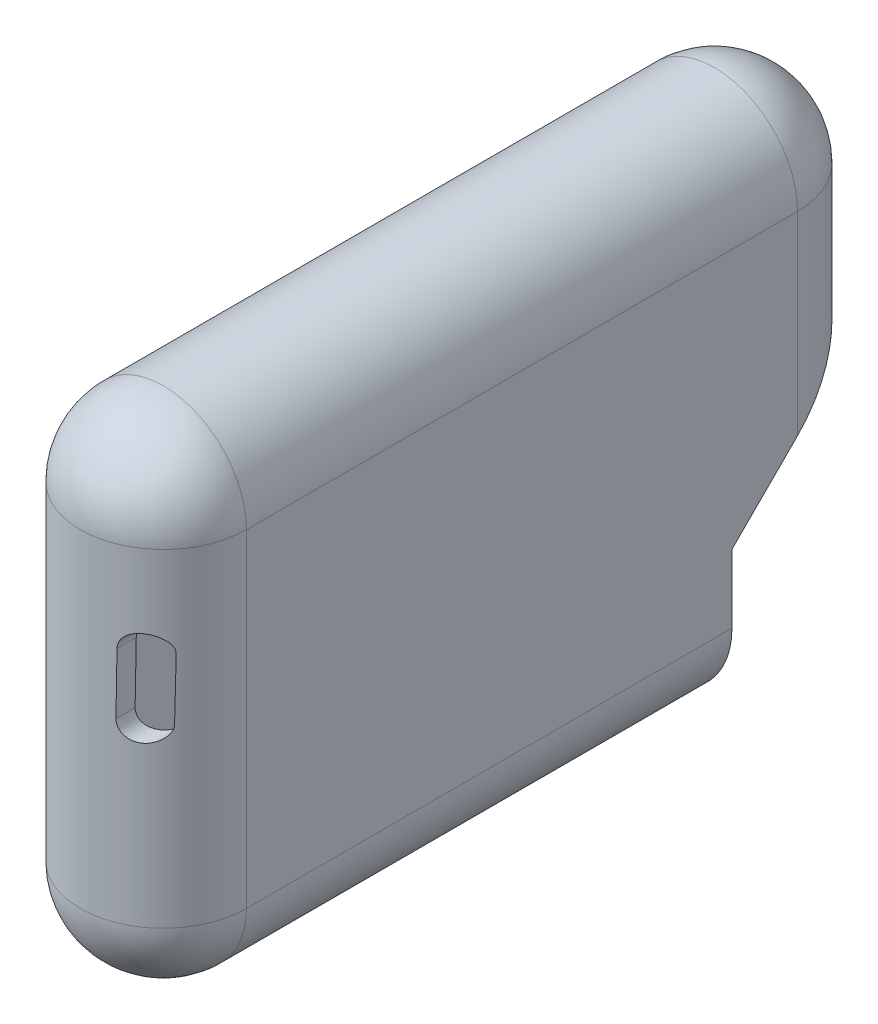
SolidWorks part; units mm, degrees
ref_plane "Front Plane" through (0, 0, 0) normal (0, 0, 1) x (1, 0, 0)
ref_plane "Top Plane" through (0, 0, 0) normal (0, 1, 0) x (1, 0, 0)
ref_plane "Right Plane" through (0, 0, 0) normal (1, 0, 0) x (0, 0, -1)
sketch "Sketch1" plane through (0, 0, 0) normal (0, 0, 1) x (1, 0, 0)
  line L0 (-1.1087, 18.0382) -> (-1.1087, -19.4618) construction
  line L5 (6.3913, 18.0382) -> (6.3913, -19.4618)
  line L6 (-8.6087, 18.0382) -> (-8.6087, -19.4618)
  arc A0 (6.3913, 18.0382) -> (-8.6087, 18.0382) centre (-1.1087, 18.0382) ccw
  arc A1 (-8.6087, -19.4618) -> (6.3913, -19.4618) centre (-1.1087, -19.4618) ccw
  point P1 (-1.1087, -0.7118)
  point P9 (0, 0)
  point P10 (7.6942, -25.282)
  point P11 (-0.4791, -20.1787)
  point P13 (-1.1087, 25.5382)
  dimension "D1" = 15
  dimension "D2" = 45
extrude "Extrude-Thin1" add sketch "Sketch1" along normal blind 8 and the other way blind 55 thin thin type one direction wall 2
sketch "Sketch3" plane through (0, 0, 8) normal (0, 0, 1) x (1, 0, 0)
  line L0 (-1.1087, 27.5382) -> (-1.1087, -28.9618) construction
  line L1 (6.3913, -19.4618) -> (6.3913, 18.0382) construction
  line L2 (8.3913, -19.4618) -> (8.3913, 18.0382) construction
  line L3 (6.3913, -19.4618) -> (6.3913, 18.0382)
  line L4 (8.3913, -19.4618) -> (8.3913, 18.0382)
  line L5 (-1.1087, 27.5382) -> (-1.1087, 25.5382)
  line L6 (-1.1087, -26.9618) -> (-1.1087, -28.9618)
  arc A0 (8.3913, 18.0382) -> (-10.6087, 18.0382) centre (-1.1087, 18.0382) ccw construction
  arc A1 (-10.6087, -19.4618) -> (8.3913, -19.4618) centre (-1.1087, -19.4618) ccw construction
  arc A2 (-8.6087, -19.4618) -> (6.3913, -19.4618) centre (-1.1087, -19.4618) ccw construction
  arc A3 (6.3913, 18.0382) -> (-8.6087, 18.0382) centre (-1.1087, 18.0382) ccw construction
  arc A4 (-1.1087, -26.9618) -> (6.3913, -19.4618) centre (-1.1087, -19.4618) ccw
  arc A5 (-1.1087, -28.9618) -> (8.3913, -19.4618) centre (-1.1087, -19.4618) ccw
  arc A6 (6.3913, 18.0382) -> (-1.1087, 25.5382) centre (-1.1087, 18.0382) ccw
  arc A7 (8.3913, 18.0382) -> (-1.1087, 27.5382) centre (-1.1087, 18.0382) ccw
revolve "Revolve1" add sketch "Sketch3" angle 180 about L0
ref_plane "Plane1" through (-1.1087, -19.4618, 17.5) normal (0, 0, 1) x (1, 0, 0)
sketch "Sketch4" plane through (-1.1087, -19.4618, 17.5) normal (0, 0, 1) x (1, 0, 0)
  line L0 (5.4685, 27.125) -> (5.3835, 20.1693) construction
  line L1 (7.4132, 27.1012) -> (7.3282, 20.1455)
  line L2 (3.5238, 27.1487) -> (3.4388, 20.193)
  arc A0 (7.4132, 27.1012) -> (3.5238, 27.1487) centre (5.4685, 27.125) ccw
  arc A1 (3.4388, 20.193) -> (7.3282, 20.1455) centre (5.3835, 20.1693) ccw
  point P4 (5.426, 23.6471)
extrude "Cut-Extrude1" cut sketch "Sketch4" against normal through all both and the other way through all
sketch "Sketch5" plane through (0, 0, -55) normal (0, 0, -1) x (-1, 0, 0)
  line L0 (1.1087, -28.9618) -> (1.1087, 27.5382) construction
  line L1 (-6.3913, -19.4618) -> (-6.3913, 18.0382) construction
  line L2 (-8.3913, -19.4618) -> (-8.3913, 18.0382) construction
  line L3 (-6.3913, -19.4618) -> (-6.3913, 18.0382)
  line L4 (-8.3913, -19.4618) -> (-8.3913, 18.0382)
  line L5 (1.1087, -28.9618) -> (1.1087, -26.9618)
  line L6 (1.1087, 25.5382) -> (1.1087, 27.5382)
  arc A0 (-8.3913, -19.4618) -> (10.6087, -19.4618) centre (1.1087, -19.4618) ccw construction
  arc A1 (10.6087, 18.0382) -> (-8.3913, 18.0382) centre (1.1087, 18.0382) ccw construction
  arc A2 (-6.3913, -19.4618) -> (8.6087, -19.4618) centre (1.1087, -19.4618) ccw construction
  arc A3 (8.6087, 18.0382) -> (-6.3913, 18.0382) centre (1.1087, 18.0382) ccw construction
  arc A4 (-6.3913, -19.4618) -> (1.1087, -26.9618) centre (1.1087, -19.4618) ccw
  arc A5 (1.1087, 25.5382) -> (-6.3913, 18.0382) centre (1.1087, 18.0382) ccw
  arc A6 (1.1087, 27.5382) -> (-8.3913, 18.0382) centre (1.1087, 18.0382) ccw
  arc A7 (-8.3913, -19.4618) -> (1.1087, -28.9618) centre (1.1087, -19.4618) ccw
revolve "Revolve2" add sketch "Sketch5" angle 180 about L0
sketch "Sketch6" plane through (8.3913, 0, 0) normal (1, 0, 0) x (0, 0, -1)
  line L0 (47.5026, -35.0618) -> (47.5026, -11.6529)
  line L1 (47.5026, -11.6529) -> (66.5493, 7.3938)
  line L5 (66.5493, 7.3938) -> (66.5493, -35.0618)
  line L6 (66.5493, -35.0618) -> (47.5026, -35.0618)
  dimension "D1" = 135
extrude "Cut-Extrude2" cut sketch "Sketch6" against normal through all both and the other way through all
